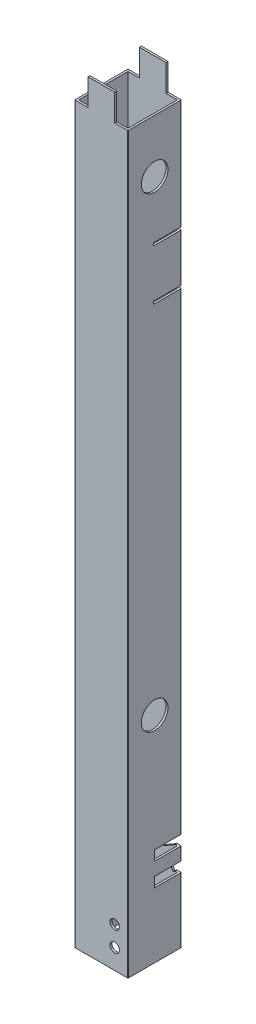
SolidWorks part; units mm, degrees
ref_plane "Front Plane" through (0, 0, 0) normal (0, 0, 1) x (1, 0, 0)
ref_plane "Top Plane" through (0, 0, 0) normal (0, 1, 0) x (1, 0, 0)
ref_plane "Right Plane" through (0, 0, 0) normal (1, 0, 0) x (0, 0, -1)
sketch "Sketch1" plane through (0, 0, 0) normal (0, 1, 0) x (1, 0, 0)
  line L0 (1.5, 1.5) -> (38.5, 1.5)
  line L1 (0.5, 0) -> (39.5, 0)
  line L2 (0, 0.5) -> (0, 39.5)
  line L3 (0.5, 40) -> (39.5, 40)
  line L4 (40, 0.5) -> (40, 39.5)
  line L5 (38.5, 1.5) -> (38.5, 38.5)
  line L6 (1.5, 38.5) -> (38.5, 38.5)
  line L7 (1.5, 1.5) -> (1.5, 38.5)
  arc A0 (39.5, 0) -> (40, 0.5) centre (39.5, 0.5) ccw
  arc A1 (0.5, 0) -> (0, 0.5) centre (0.5, 0.5) cw
  arc A2 (0, 39.5) -> (0.5, 40) centre (0.5, 39.5) cw
  arc A3 (39.5, 40) -> (40, 39.5) centre (39.5, 39.5) cw
  arc A4 (38.5, 1.5) -> (38.5, 1.5) centre (38.5, 1.5) ccw
  arc A5 (38.5, 38.5) -> (38.5, 38.5) centre (38.5, 38.5) cw
  arc A6 (1.5, 38.5) -> (1.5, 38.5) centre (1.5, 38.5) cw
  arc A7 (1.5, 1.5) -> (1.5, 1.5) centre (1.5, 1.5) cw
  point P9 (0, 0)
  dimension "D3" = 0.5
  dimension "D1" = 40
  dimension "D2" = 40
  dimension "D4" = 1.5
extrude "Boss-Extrude1" add sketch "Sketch1" along normal blind 571
sketch "Sketch2" plane through (0, 0, -40) normal (0, 0, 1) x (1, 0, 0)
  line L0 (0.5, 571) -> (39.5, 571) construction
  line L11 (30, 571) -> (40, 571)
  line L12 (30, 571) -> (30, 551)
  line L13 (30, 551) -> (40, 551)
  line L14 (40, 571) -> (40, 551)
  line L15 (40, 571) -> (40, 0) construction
  line L16 (20, 571) -> (20, 1571.1839) construction
  line L17 (0, 571) -> (0, 551)
  line L18 (10, 551) -> (0, 551)
  line L19 (10, 571) -> (10, 551)
  line L20 (10, 571) -> (0, 571)
  dimension "D1" = 20
  dimension "D2" = 10
extrude "Cut-Extrude1" cut sketch "Sketch2" along normal blind 40
sketch "Sketch3" plane through (40, 0, 0) normal (1, 0, 0) x (0, 0, -1)
  line L0 (40, 551) -> (40, 0) construction
  line L5 (19, 468.5) -> (40, 468.5)
  line L7 (19, 468.5) -> (19, 466.5)
  line L17 (19, 466.5) -> (40, 466.5)
  line L22 (40, 468.5) -> (40, 466.5)
  line L23 (0.5, 551) -> (39.5, 551) construction
  line L24 (40, 448.5) -> (21.8195, 448.5) construction
  line L25 (40, 428.5) -> (40, 430.5)
  line L26 (19, 430.5) -> (40, 430.5)
  line L27 (19, 428.5) -> (19, 430.5)
  line L28 (19, 428.5) -> (40, 428.5)
  dimension "D1" = 2
  dimension "D2" = 21
  dimension "D3" = 82.5
  dimension "D4" = 20
extrude "Cut-Extrude2" cut sketch "Sketch3" against normal blind 20
sketch "Sketch4" plane through (0, 0, -40) normal (0, 0, -1) x (-1, 0, 0)
  line L5 (-37, 71.8678) -> (-40, 73.5999) construction
  line L16 (-40, 73.5999) -> (-40.775, 74.0473) construction
  line L30 (-40, 50.5059) -> (-35.2267, 47.75) construction
  line L32 (-40, 73.5999) -> (-37, 73.5999)
  line L36 (-37, 73.5999) -> (-37, 71.8678)
  line L38 (-37, 71.8678) -> (-25.6597, 65.3205)
  line L50 (-25.6597, 65.3205) -> (-28.1597, 60.9904)
  line L55 (-20, 0) -> (-20, 25.0728) construction
  line L58 (-28.1597, 60.9904) -> (-37, 66.0943)
  line L59 (-37, 66.0943) -> (-40, 66.0943)
  line L62 (-39.5, 0) -> (-0.5, 0) construction
  line L80 (-40, 66.0943) -> (-40, 73.5999)
  line L81 (-40, 56.2794) -> (-37, 56.2794)
  line L82 (-37, 56.2794) -> (-37, 54.5473)
  line L83 (-37, 54.5473) -> (-32.7267, 52.0801)
  line L84 (-37, 48.7738) -> (-40, 48.7738)
  line L85 (-40, 48.7738) -> (-40, 56.2794)
  line L86 (-37, 48.7738) -> (-35.2267, 47.75)
  line L87 (-35.2267, 47.75) -> (-32.7267, 52.0801)
extrude "Cut-Extrude3" cut sketch "Sketch4" against normal blind 20
sketch "Sketch5" plane through (0, 0, 0) normal (0, 0, 1) x (1, 0, 0)
  line L0 (0.5, 0) -> (39.5, 0) construction
  line L1 (40, 551) -> (40, 0) construction
  circle A0 centre (30, 15) radius 3.5
  circle A1 centre (30, 30) radius 3.5
  dimension "D1" = 15
  dimension "D2" = 15
  dimension "D3" = 7
  dimension "D4" = 10
extrude "Cut-Extrude4" cut sketch "Sketch5" against normal blind 10
sketch "Sketch6" plane through (0, 0, 0) normal (-1, 0, 0) x (0, 0, 1)
  line L0 (-0.5, 551) -> (-39.5, 551) construction
  circle A0 centre (-20, 511) radius 10
  circle A1 centre (-20, 161) radius 10
  point P4 (0, 0)
  point P5 (-20, 551)
  point P8 (0, 0)
  dimension "D1" = 40
  dimension "D2" = 20
  dimension "D3" = 350
extrude "Cut-Extrude5" cut sketch "Sketch6" against normal through all
